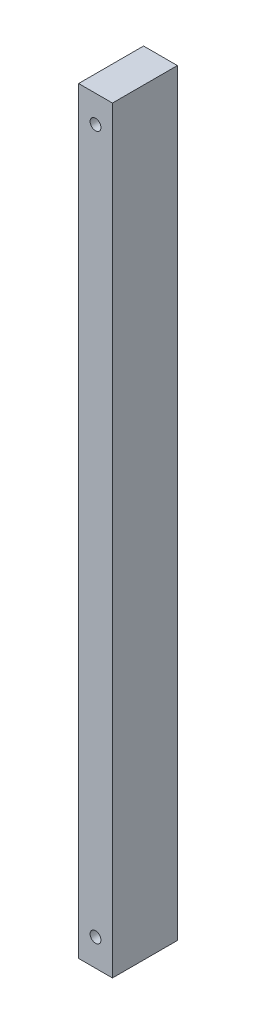
SolidWorks part; units mm, degrees
material "Pine"
ref_plane "Front Plane" through (0, 0, 0) normal (0, 0, 1) x (1, 0, 0)
ref_plane "Top Plane" through (0, 0, 0) normal (0, 1, 0) x (1, 0, 0)
ref_plane "Right Plane" through (0, 0, 0) normal (1, 0, 0) x (0, 0, -1)
sketch "Sketch1" plane through (0, 0, 0) normal (1, 0, 0) x (0, 0, -1)
  line L1 (0, 0) -> (38.1, 0)
  line L2 (0, 0) -> (0, 444.5)
  line L3 (0, 444.5) -> (38.1, 444.5)
  line L4 (38.1, 0) -> (38.1, 444.5)
  dimension "D1" = 444.5
  dimension "D2" = 38.1
extrude "Boss-Extrude1" add sketch "Sketch1" along normal blind 19.8438
sketch "Sketch2" plane through (0, 0, 0) normal (0, 0, 1) x (1, 0, 0)
  line L0 (9.9219, 444.5) -> (9.9219, 0) construction
  line L1 (19.8438, 444.5) -> (0, 444.5) construction
  line L2 (19.8438, 0) -> (0, 0) construction
  circle A0 centre (9.9219, 15.875) radius 3.175
  circle A1 centre (9.9219, 428.625) radius 3.175
  dimension "D2" = 6.35
  dimension "D4" = 6.35
  dimension "D1" = 15.875
  dimension "D3" = 15.875
extrude "Cut-Extrude1" cut sketch "Sketch2" against normal through all
